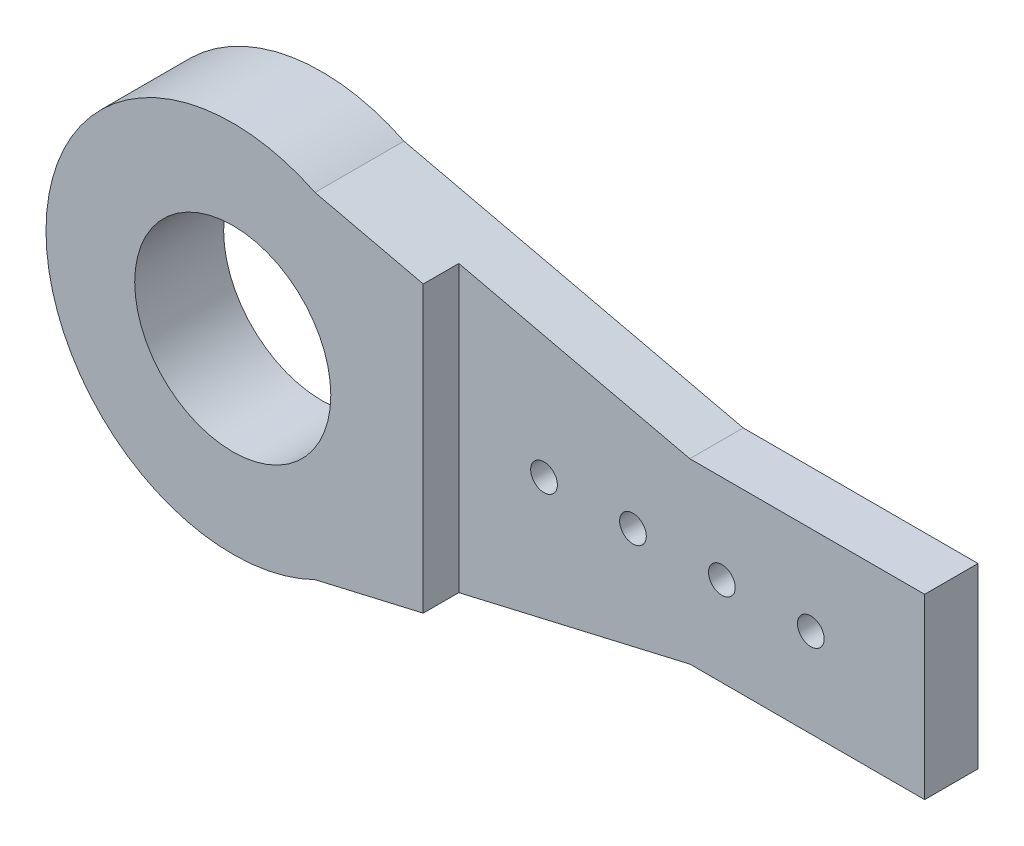
SolidWorks part; units mm, degrees
ref_plane "Ön Düzlem" through (0, 0, 0) normal (0, 0, 1) x (1, 0, 0)
ref_plane "Üst Düzlem" through (0, 0, 0) normal (0, 1, 0) x (1, 0, 0)
ref_plane "Sağ Düzlem" through (0, 0, 0) normal (1, 0, 0) x (0, 0, -1)
sketch "Çizim1" plane through (0, 0, 0) normal (0, 0, 1) x (1, 0, 0)
  line L0 (-38.1513, 18.8537) -> (0, 10)
  line L1 (0, 10) -> (26.4, 10)
  line L3 (0, -10) -> (26.4, -10)
  line L4 (26.4, 10) -> (26.4, -10)
  line L5 (0, 0) -> (26.4, -10) construction
  line L6 (0, 0) -> (26.4, 10) construction
  line L7 (-38.1513, -18.8537) -> (0, -10)
  line L8 (-47.4, 2.3639) -> (-47.4, -2.5121) construction
  arc A0 (-38.1513, 18.8537) -> (-38.1513, -18.8537) centre (-47.4, 0) ccw
  circle A1 centre (-47.4, 0) radius 7.5
  circle A2 centre (-16.4, 0) radius 1.5
  circle A6 centre (-6.4, 0) radius 1.5
  circle A7 centre (3.6, 0) radius 1.5
  circle A8 centre (13.6, 0) radius 1.5
  point P0 (0, 0)
  dimension "D3" = 42
  dimension "D4" = 15
  dimension "D5" = 3
  dimension "D6" = 3
  dimension "D7" = 3
  dimension "D8" = 3
  dimension "D10" = 10
  dimension "D11" = 10
  dimension "D12" = 10
  dimension "D1" = 20
extrude "Yükseklik-Ekstrüzyon1" add sketch "Çizim1" along normal blind 10
sketch "Çizim2" plane through (0, 0, 10) normal (0, 0, 1) x (1, 0, 0)
  line L0 (-38.1513, -18.8537) -> (0, -10) construction
  line L1 (0, -10) -> (26.4, -10) construction
  line L2 (26.4, -10) -> (26.4, 10) construction
  line L3 (26.4, 10) -> (0, 10) construction
  line L4 (0, 10) -> (-38.1513, 18.8537) construction
  line L5 (-25.98, -16.0291) -> (0, -10)
  line L6 (0, -10) -> (26.4, -10)
  line L7 (26.4, -10) -> (26.4, 10)
  line L8 (26.4, 10) -> (0, 10)
  line L9 (0, 10) -> (-25.98, 16.0291)
  line L10 (-25.98, 16.0291) -> (-25.98, -16.0291)
  dimension "D1" = 52.38
extrude "Kes-Ekstrüzyon1" cut sketch "Çizim2" against normal blind 4
sketch "Çizim3" plane through (0, 0, 10) normal (0, 0, 1) x (1, 0, 0)
  circle A0 centre (-47.4, 0) radius 11.025
  dimension "D1" = 22.05
extrude "Kes-Ekstrüzyon2" cut sketch "Çizim3" against normal blind 69
